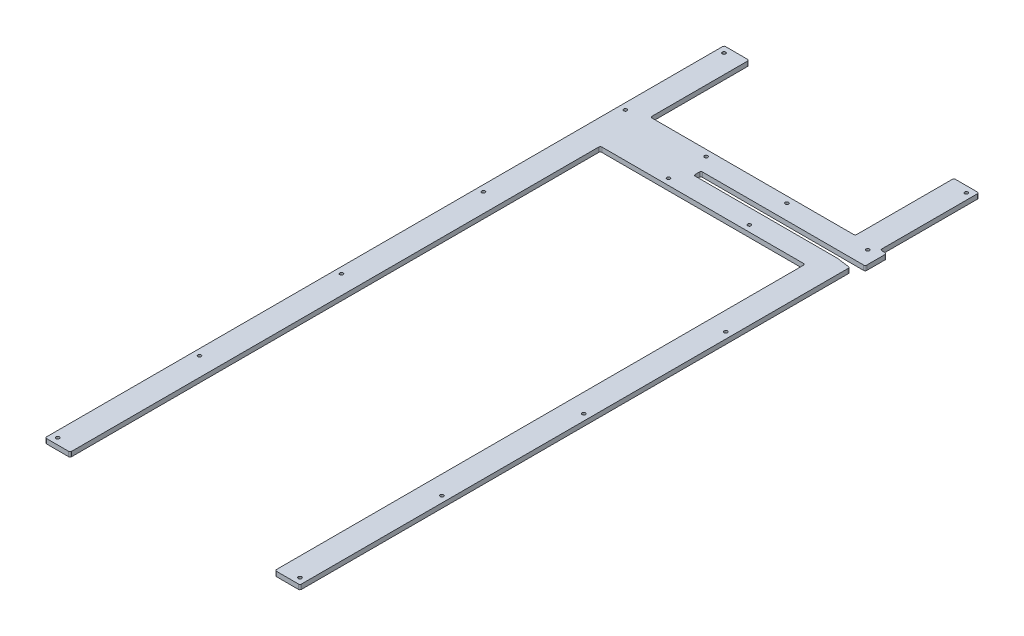
SolidWorks part; units mm, degrees
material "PE Low/Medium Density"
ref_plane "Front Plane" through (0, 0, 0) normal (0, 0, 1) x (1, 0, 0)
ref_plane "Top Plane" through (0, 0, 0) normal (0, 1, 0) x (1, 0, 0)
ref_plane "Right Plane" through (0, 0, 0) normal (1, 0, 0) x (0, 0, -1)
sketch "Sketch1" plane through (0, 0, 0) normal (0, 1, 0) x (1, 0, 0)
  line L0 (-258.3, 0) -> (-207.5, 0)
  line L1 (-207.5, 0) -> (-207.5, 1074.4)
  line L2 (-207.5, 1074.4) -> (207.5, 1074.4)
  line L3 (207.5, 1074.4) -> (207.5, 0)
  line L4 (207.5, 0) -> (258.3, 0)
  line L5 (258.3, 0) -> (258.3, 1113.9149)
  line L6 (230.3, 1117.85) -> (-61.7, 1117.85)
  line L7 (-61.7, 1117.85) -> (-61.7, 1132.55)
  line L8 (-61.7, 1132.55) -> (271.3, 1132.55)
  line L9 (271.3, 1132.55) -> (271.3, 1176)
  line L10 (271.3, 1176) -> (-258.3, 1176)
  line L11 (-258.3, 1176) -> (-258.3, 0)
  line L12 (-207.5, 0) -> (207.5, 0) construction
  line L13 (-182.147, 1176) -> (-182.147, 1074.4) construction
  line L14 (-61.7, 1125.2) -> (-162.228, 1125.2) construction
  line L15 (230.3, 1117.85) -> (258.3, 1113.9149)
  point P0 (0, 0)
  point P18 (-182.147, 1125.2)
  dimension "D1" = 516.6
  dimension "D2" = 1176
  dimension "D3" = 50.8
  dimension "D4" = 101.6
  dimension "D5" = 14.7
  dimension "D6" = 320
  dimension "D7" = 13
  dimension "D8" = 8
  dimension "D9" = 28
extrude "Boss-Extrude1" add sketch "Sketch1" along normal blind 9.525
sketch "Sketch4" plane through (0, 0, 0) normal (0, -1, 0) x (1, 0, 0)
  line L0 (271.3, -1176) -> (-258.3, -1176) construction
  line L1 (-258.3, -1176) -> (-207.5, -1176)
  line L2 (-258.3, -1176) -> (-258.3, -1376)
  line L3 (-258.3, -1376) -> (-207.5, -1376)
  line L4 (-207.5, -1176) -> (-207.5, -1376)
  line L5 (258.3, -1176) -> (207.5, -1176)
  line L6 (258.3, -1176) -> (258.3, -1376)
  line L7 (258.3, -1376) -> (207.5, -1376)
  line L8 (207.5, -1176) -> (207.5, -1376)
  line L9 (258.3, 0) -> (258.3, -1113.9149) construction
  line L10 (207.5, -1074.4) -> (207.5, 0) construction
  line L11 (-207.5, 0) -> (-207.5, -1074.4) construction
  dimension "D1" = 200
extrude "Boss-Extrude2" add sketch "Sketch4" against normal up to surface (9.525 mm away) up to face at (49.9615, 9.525, -778.1165)
hole_wizard "CSK for 1/4 Flat Head Machine Screw (100)1" positions "Sketch3" profile "Sketch2" countersink size "1/4" standard "Ansi Inch" end condition through all
sketch "Sketch3" plane through (0, 0, 0) normal (0, -1, 0) x (1, 0, 0)
  line L0 (271.3, -1176) -> (258.3, -1176) construction
  line L1 (-258.3, -1376) -> (-258.3, 0) construction
  point P0 (-245.6, -1163.3)
  dimension "D1" = 12.7
  dimension "D2" = 12.7
sketch "Sketch2" plane through (-245.6, 0, -1163.3) normal (1, 0, 0) x (0, 0, -1)
  line L0 (0, 0) -> (0, 9.525)
  line L1 (0, 9.525) -> (3.3782, 9.525)
  line L2 (3.3782, 9.525) -> (3.3782, 4.5682)
  line L3 (3.3782, 4.5682) -> (8.8224, 0)
  line L5 (8.8224, 0) -> (0, 0)
  line L6 (-3.3782, 4.5682) -> (-8.8224, 0) construction
  line L11 (0, -6.35) -> (0, 107.95) construction
  dimension "Thru Hole Dia." = 6.7564
  dimension "Thru Hole Depth" = 9.5251
  dimension "Near C'Sink Dia." = 17.6448
  dimension "Near C'Sink Angle" = 100
pattern_linear "LPattern1" count 2 spacing 491.2 along (1, 0, 0) count 5 spacing 287.65 along (0, 0, 1) of "CSK for 1/4 Flat Head Machine Screw (100)1"
pattern_linear "LPattern2" count 3 spacing 163.7333 along (1, 0, 0) count 2 spacing 76.2 along (0, 0, 1) skipping (0, 1) of "CSK for 1/4 Flat Head Machine Screw (100)1"
hole_wizard "CSK for 1/4 Flat Head Machine Screw (100)2" positions "Sketch6" profile "Sketch5" countersink size "1/4" standard "Ansi Inch" end condition through all
sketch "Sketch6" plane through (0, 0, 0) normal (0, -1, 0) x (1, 0, 0)
  line L0 (-258.3, -1376) -> (-207.5, -1376) construction
  line L1 (-258.3, -1376) -> (-258.3, 0) construction
  point P0 (-245.6, -1363.3)
  dimension "D1" = 12.7
  dimension "D2" = 12.7
sketch "Sketch5" plane through (-245.6, 0, -1363.3) normal (1, 0, 0) x (0, 0, -1)
  line L0 (0, 0) -> (0, 9.525)
  line L1 (0, 9.525) -> (3.3782, 9.525)
  line L2 (3.3782, 9.525) -> (3.3782, 4.5682)
  line L3 (3.3782, 4.5682) -> (8.8224, 0)
  line L5 (8.8224, 0) -> (0, 0)
  line L6 (-3.3782, 4.5682) -> (-8.8224, 0) construction
  line L11 (0, -6.35) -> (0, 107.95) construction
  dimension "Thru Hole Dia." = 6.7564
  dimension "Thru Hole Depth" = 9.5251
  dimension "Near C'Sink Dia." = 17.6448
  dimension "Near C'Sink Angle" = 100
mirror "Mirror1" about plane through (0, 0, 0) normal (1, 0, 0) of "CSK for 1/4 Flat Head Machine Screw (100)2"
fillet "Fillet1" radius 3.175 11 edges at (258.3, 4.7625, 0) (207.5, 4.7625, 0) (-207.5, 4.7625, 0) (-258.3, 4.7625, 0) (207.5, 4.7625, -1074.4) (-207.5, 4.7625, -1074.4) (258.3, 4.7625, -1113.9149) (271.3, 4.7625, -1132.55) (271.3, 4.7625, -1176) (-61.7, 4.7625, -1117.85) (-61.7, 4.7625, -1132.55)
fillet "Fillet2" radius 3.175 7 edges at (207.5, 4.7625, -1376) (258.3, 4.7625, -1376) (-258.3, 4.7625, -1376) (-207.5, 4.7625, -1376) (207.5, 4.7625, -1176) (258.3, 4.7625, -1176)
